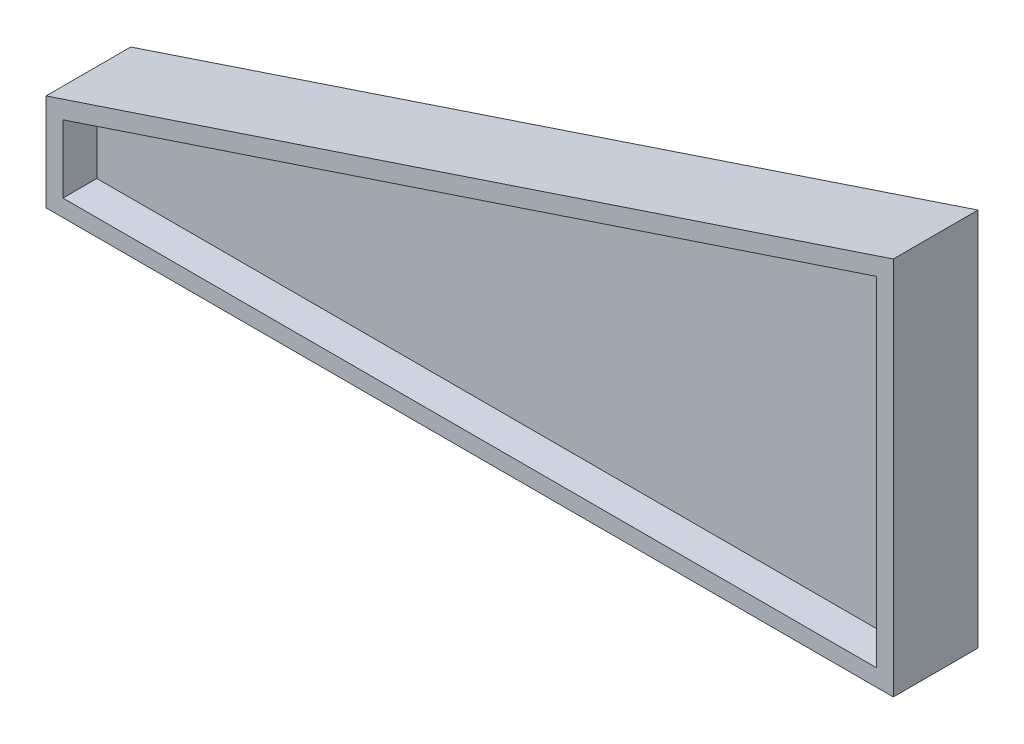
SolidWorks part; units mm, degrees
ref_plane "Front Plane" through (0, 0, 0) normal (0, 0, 1) x (1, 0, 0)
ref_plane "Top Plane" through (0, 0, 0) normal (0, 1, 0) x (1, 0, 0)
ref_plane "Right Plane" through (0, 0, 0) normal (1, 0, 0) x (0, 0, -1)
sketch "Sketch1" plane through (0, 0, 0) normal (0, 0, 1) x (1, 0, 0)
  line L0 (0, 0) -> (0, 254)
  line L1 (0, 254) -> (-609.6, 50.8)
  line L2 (-609.6, 50.8) -> (-609.6, 0)
  line L3 (-609.6, 0) -> (0, 0)
  point P3 (-968.9171, 50.8)
  dimension "D1" = 50.8
  dimension "D2" = 609.6
  dimension "D3" = 254
extrude "Boss-Extrude1" add sketch "Sketch1" along normal blind 12.7
sketch "Sketch2" plane through (0, 0, 12.7) normal (0, 0, 1) x (1, 0, 0)
  line L14 (0, 254) -> (-609.6, 50.8)
  line L15 (-609.6, 50.8) -> (-609.6, 0)
  line L16 (-609.6, 0) -> (0, 0)
  line L17 (0, 0) -> (0, 254)
  line L18 (12.7, -12.7) -> (12.7, 271.6203)
  line L19 (-622.3, -12.7) -> (12.7, -12.7)
  line L20 (-622.3, 59.9536) -> (-622.3, -12.7)
  line L21 (12.7, 271.6203) -> (-622.3, 59.9536)
  line L22 (12.7, -12.7) -> (12.7, 271.6203)
  line L23 (-622.3, -12.7) -> (12.7, -12.7)
  line L24 (-622.3, 59.9536) -> (-622.3, -12.7)
  line L25 (12.7, 271.6203) -> (-622.3, 59.9536)
  dimension "D1" = 12.7
extrude "Boss-Extrude2" add sketch "Sketch2" along normal blind 25.4 and the other way blind 38.1
